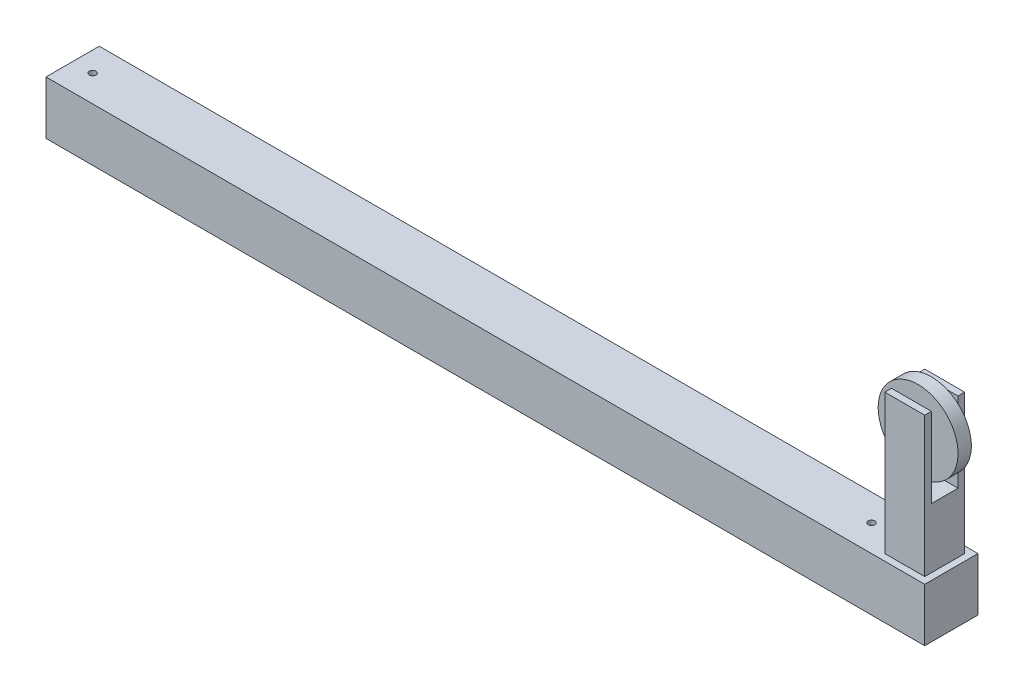
SolidWorks part; units mm, degrees
ref_plane "Front Plane" through (0, 0, 0) normal (0, 0, 1) x (1, 0, 0)
ref_plane "Top Plane" through (0, 0, 0) normal (0, 1, 0) x (1, 0, 0)
ref_plane "Right Plane" through (0, 0, 0) normal (1, 0, 0) x (0, 0, -1)
sketch "Sketch1" plane through (0, 0, 0) normal (0, 0, 1) x (1, 0, 0)
  line L1 (0, 0) -> (1676.4, 0)
  line L2 (0, 0) -> (0, 101.6)
  line L3 (0, 101.6) -> (1676.4, 101.6)
  line L4 (1676.4, 0) -> (1676.4, 101.6)
  dimension "D1" = 101.6
  dimension "D2" = 1676.4
extrude "Boss-Extrude1" add sketch "Sketch1" along normal blind 101.6 contours L2 L3 L4 L1
sketch "Sketch3" plane through (0, 0, 0) normal (-1, 0, 0) x (0, 0, 1)
  line L0 (101.6, 101.6) -> (0, 101.6) construction
  line L1 (12.7, 12.7) -> (88.9, 12.7)
  line L2 (12.7, 12.7) -> (12.7, 88.9)
  line L3 (12.7, 88.9) -> (88.9, 88.9)
  line L4 (88.9, 12.7) -> (88.9, 88.9)
  line L5 (101.6, 0) -> (101.6, 101.6) construction
  dimension "D1" = 76.2
  dimension "D2" = 12.7
  dimension "D3" = 12.7
extrude "Cut-Extrude1" cut sketch "Sketch3" against normal blind 127
sketch "Sketch5" plane through (0, 101.6, 0) normal (0, 1, 0) x (1, 0, 0)
  line L0 (0, 0) -> (1676.4, 0) construction
  line L1 (1587.5, -88.9) -> (1663.7, -88.9)
  line L2 (1587.5, -88.9) -> (1587.5, -12.7)
  line L3 (1587.5, -12.7) -> (1663.7, -12.7)
  line L4 (1663.7, -88.9) -> (1663.7, -12.7)
  line L5 (1676.4, -101.6) -> (1676.4, 0) construction
  dimension "D1" = 76.2
  dimension "D2" = 76.2
  dimension "D3" = 12.7
  dimension "D4" = 12.7
extrude "Boss-Extrude2" add sketch "Sketch5" along normal blind 114.3
sketch "Sketch6" plane through (0, 215.9, 0) normal (0, 1, 0) x (1, 0, 0)
  line L0 (1663.7, -12.7) -> (1587.5, -12.7) construction
  line L1 (1587.5, -12.7) -> (1663.7, -12.7)
  line L2 (1587.5, -12.7) -> (1587.5, -25.4)
  line L3 (1587.5, -25.4) -> (1663.7, -25.4)
  line L4 (1663.7, -12.7) -> (1663.7, -25.4)
  line L5 (1663.7, -12.7) -> (1587.5, -12.7) construction
  line L6 (1663.7, -88.9) -> (1663.7, -12.7) construction
  line L7 (1587.5, -12.7) -> (1587.5, -88.9) construction
  line L8 (1663.7, -88.9) -> (1587.5, -88.9)
  line L9 (1663.7, -88.9) -> (1663.7, -76.2)
  line L10 (1663.7, -76.2) -> (1587.5, -76.2)
  line L11 (1587.5, -88.9) -> (1587.5, -76.2)
  line L12 (1587.5, -12.7) -> (1587.5, -88.9) construction
  dimension "D1" = 12.7
  dimension "D2" = 12.7
extrude "Boss-Extrude3" add sketch "Sketch6" along normal blind 152.4
ref_plane "Plane1" through (0, 0, 50.8) normal (0, 0, -1) x (-1, 0, 0)
sketch "Sketch7" plane through (0, 0, 50.8) normal (0, 0, -1) x (-1, 0, 0)
  line L0 (-1663.7, 368.3) -> (-1663.7, 101.6) construction
  line L1 (-1663.7, 368.3) -> (-1587.5, 368.3) construction
  circle A0 centre (-1625.6, 311.15) radius 12.7
  dimension "D1" = 25.4
  dimension "D2" = 38.1
  dimension "D3" = 57.15
extrude "Boss-Extrude4" add sketch "Sketch7" along normal up to surface and the other way up to surface up to face at (1625.6, 292.1, 25.4) other way up to face at (1625.6, 292.1, 76.2)
sketch "Sketch8" plane through (0, 0, 50.8) normal (0, 0, -1) x (-1, 0, 0)
  line L0 (-1663.7, 368.3) -> (-1663.7, 101.6) construction
  line L1 (-1663.7, 368.3) -> (-1587.5, 368.3) construction
  circle A0 centre (-1625.6, 311.15) radius 76.2
  dimension "D1" = 152.4
  dimension "D2" = 38.1
  dimension "D3" = 57.15
extrude "Boss-Extrude5" add sketch "Sketch8" along normal blind 12.7 and the other way blind 12.7
sketch "Sketch9" plane through (0, 101.6, 0) normal (0, 1, 0) x (1, 0, 0)
  line L0 (55.88, -50.8) -> (-55.88, -50.8) construction
  line L1 (0, -101.6) -> (0, 0) construction
  line L2 (1587.5, -12.7) -> (1587.5, -88.9) construction
  circle A0 centre (38.1, -50.8) radius 6.35
  circle A1 centre (1524, -50.8) radius 6.35
  dimension "D1" = 12.7
  dimension "D2" = 12.7
  dimension "D3" = 38.1
  dimension "D4" = 63.5
extrude "Cut-Extrude2" cut sketch "Sketch9" against normal up to surface (12.7 mm away) up to face at (63.5, 88.9, 50.8)
